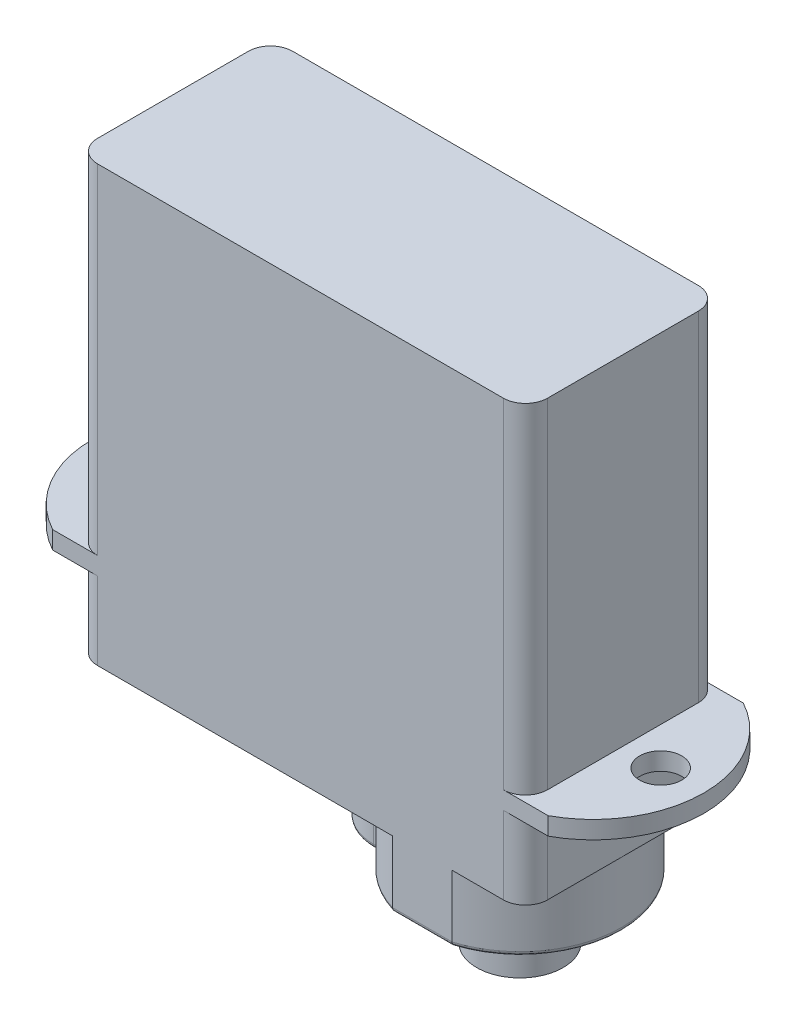
SolidWorks part; units mm, degrees
ref_plane "Спереди" through (0, 0, 0) normal (0, 0, 1) x (1, 0, 0)
ref_plane "Сверху" through (0, 0, 0) normal (0, 1, 0) x (1, 0, 0)
ref_plane "Справа" through (0, 0, 0) normal (1, 0, 0) x (0, 0, -1)
sketch "Эскиз1" plane through (0, 0, 0) normal (0, 1, 0) x (1, 0, 0)
  line L1 (-9.15, -4.4) -> (9.15, -4.4)
  line L2 (-10.15, -3.4) -> (-10.15, 3.4)
  line L3 (-9.15, 4.4) -> (9.15, 4.4)
  line L4 (10.15, -3.4) -> (10.15, 3.4)
  line L5 (-10.15, -4.4) -> (10.15, 4.4) construction
  line L6 (-10.15, 4.4) -> (10.15, -4.4) construction
  arc A0 (-10.15, -3.4) -> (-9.15, -4.4) centre (-9.15, -3.4) ccw
  arc A1 (9.15, -4.4) -> (10.15, -3.4) centre (9.15, -3.4) ccw
  arc A2 (10.15, 3.4) -> (9.15, 4.4) centre (9.15, 3.4) ccw
  arc A3 (-9.15, 4.4) -> (-10.15, 3.4) centre (-9.15, 3.4) ccw
  point P0 (0, 0)
  dimension "D3" = 1
  dimension "D1" = 20.3
  dimension "D2" = 8.8
extrude "Бобышка-Вытянуть1" add sketch "Эскиз1" along normal blind 19.6
sketch "Эскиз2" plane through (0, 0, 0) normal (0, -1, 0) x (1, 0, 0)
  line L0 (-11.1749, 4.4) -> (11.1749, 4.4)
  line L1 (-9.15, 4.4) -> (9.15, 4.4) construction
  line L2 (-11.1749, -4.4) -> (11.1749, -4.4)
  line L3 (9.15, -4.4) -> (-9.15, -4.4) construction
  line L4 (-13.8, 0) -> (-13.8, 4.4) construction
  line L5 (13.8, 0) -> (13.8, 4.4) construction
  arc A0 (11.1749, 4.4) -> (11.1749, -4.4) centre (8.8, 0) cw
  arc A1 (-11.1749, 4.4) -> (-11.1749, -4.4) centre (-8.8, 0) ccw
  point P8 (0, 4.4)
  point P9 (0, -4.4)
  arc M1 (-9.15, 4.4) -> (-10.15, 3.4) centre (-9.15, 3.4) ccw
  line M2 (-10.15, 3.4) -> (-10.15, -3.4)
  arc M3 (-10.15, -3.4) -> (-9.15, -4.4) centre (-9.15, -3.4) ccw
  arc M5 (9.15, -4.4) -> (10.15, -3.4) centre (9.15, -3.4) ccw
  line M6 (10.15, -3.4) -> (10.15, 3.4)
  arc M7 (10.15, 3.4) -> (9.15, 4.4) centre (9.15, 3.4) ccw
  dimension "D2" = 5
  dimension "D1" = 27.6
extrude "Бобышка-Вытянуть2" add sketch "Эскиз2" against normal blind 0.8 from offset 3.5 contours L0 A1 L2 M3 M2 M1 | A0 L0 L2 M7 M6 M5
sketch "Эскиз3" plane through (0, 0, 0) normal (0, -1, 0) x (1, 0, 0)
  line L0 (1.5456, 2.35) -> (1.25, 2.35)
  line L1 (1.5456, -2.35) -> (1.25, -2.35)
  line L2 (-1.1, 0) -> (-1.1, 4.4) construction
  line L3 (-9.15, 4.4) -> (9.15, 4.4) construction
  line L4 (10.1, 0) -> (10.1, 4.4) construction
  line L6 (9.15, 4.4) -> (11.1749, 4.4) construction
  arc A0 (1.5456, -2.35) -> (1.5456, 2.35) centre (5.5, 0) ccw
  arc A1 (1.25, 2.35) -> (1.25, -2.35) centre (1.25, 0) ccw
  line M4 (-9.15, -4.4) -> (9.15, -4.4)
  line M8 (9.15, 4.4) -> (-9.15, 4.4)
  dimension "D1" = 4.6
  dimension "D2" = 5.5
  dimension "D3" = 4.7
  dimension "D4" = 11.2
extrude "Бобышка-Вытянуть3" add sketch "Эскиз3" along normal blind 3 contours L0 A1 L1 A0 M4 M8
fillet "Скругление1" radius 0.2 8 edges at (-1.1, -3, 0) (2.6605, -3, -3.619) (5.5, -3, -4.4) (10.1, -3, 0) (5.5, -3, 4.4) (2.6605, -3, 3.619) (1.3978, -3, -2.35) (1.3978, -3, 2.35)
sketch "Эскиз4" plane through (0, -3, 0) normal (0, -1, 0) x (1, 0, 0)
  circle A0 centre (5.5, 0) radius 1.95
  circle A1 centre (5.5, 0) radius 0.75
  dimension "D1" = 3.9
  dimension "D2" = 1.5
extrude "Бобышка-Вытянуть4" add sketch "Эскиз4" along normal blind 2.7
sketch "Эскиз5" plane through (0, 3.5, 0) normal (0, -1, 0) x (1, 0, 0)
  circle A0 centre (-11.85, 0) radius 0.95
  circle A1 centre (11.85, 0) radius 0.95
  dimension "D1" = 23.7
  dimension "D2" = 1.9
  dimension "D3" = 11.85
extrude "Вырез-Вытянуть1" cut sketch "Эскиз5" against normal up to next
